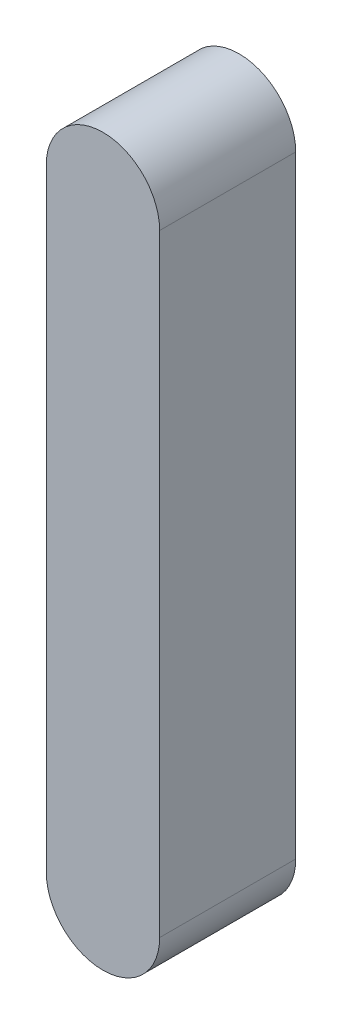
SolidWorks part; units mm, degrees
ref_plane "前视基准面" through (0, 0, 0) normal (0, 0, 1) x (1, 0, 0)
ref_plane "上视基准面" through (0, 0, 0) normal (0, 1, 0) x (1, 0, 0)
ref_plane "右视基准面" through (0, 0, 0) normal (1, 0, 0) x (0, 0, -1)
sketch "草图1" plane through (0, 0, 0) normal (0, 0, 1) x (1, 0, 0)
  line L0 (0, 0) -> (0, 135) construction
  line L1 (-12.5, 0) -> (-12.5, 135)
  line L2 (12.5, 0) -> (12.5, 135)
  arc A0 (-12.5, 0) -> (12.5, 0) centre (0, 0) ccw
  arc A1 (12.5, 135) -> (-12.5, 135) centre (0, 135) ccw
  point P3 (0, 67.5)
  dimension "D1" = 135
  dimension "D2" = 25
extrude "凸台-拉伸1" add sketch "草图1" along normal mid plane 30
